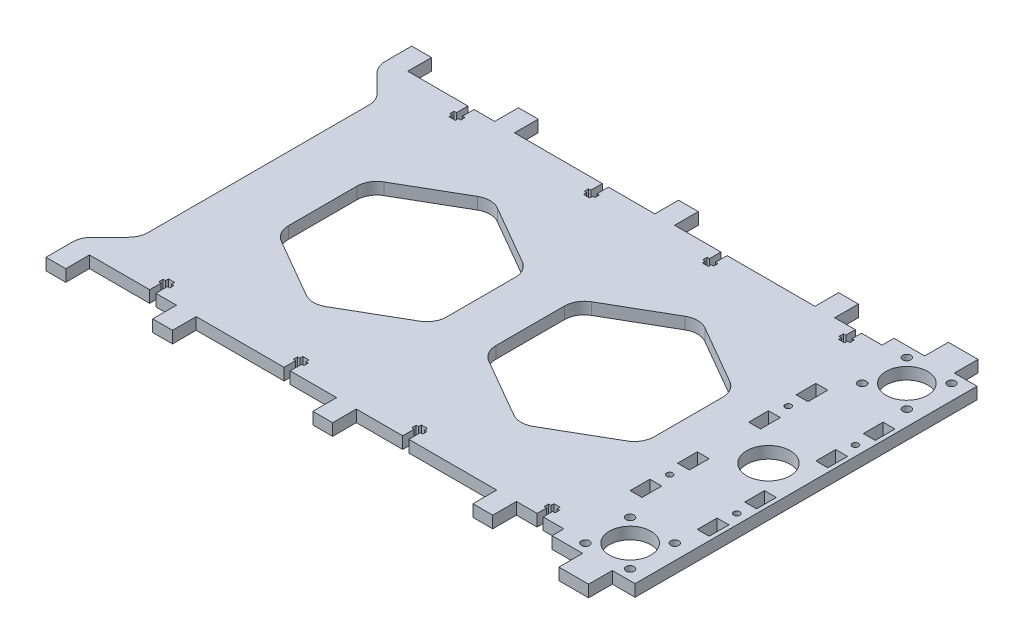
SolidWorks part; units mm, degrees
ref_plane "Спереди" through (0, 0, 0) normal (0, 0, 1) x (1, 0, 0)
ref_plane "Сверху" through (0, 0, 0) normal (0, 1, 0) x (1, 0, 0)
ref_plane "Справа" through (0, 0, 0) normal (1, 0, 0) x (0, 0, -1)
sketch "Эскиз1" plane through (0, 0, 0) normal (0, 1, 0) x (1, 0, 0)
  line L0 (138.7789, 22.6105) -> (144.7789, 22.6105)
  line L1 (138.7789, 12.6105) -> (138.7789, 22.6105)
  line L2 (144.7789, 12.6105) -> (138.7789, 12.6105)
  line L3 (144.7789, 22.6105) -> (144.7789, 12.6105)
  line L4 (138.7789, 36.6105) -> (138.7789, 46.6105)
  line L5 (144.7789, 36.6105) -> (138.7789, 36.6105)
  line L6 (144.7789, 46.6105) -> (144.7789, 36.6105)
  line L7 (138.7789, 46.6105) -> (144.7789, 46.6105)
  line L8 (104.7789, 46.6105) -> (110.7789, 46.6105)
  line L9 (104.7789, 36.6105) -> (104.7789, 46.6105)
  line L10 (110.7789, 36.6105) -> (104.7789, 36.6105)
  line L11 (110.7789, 46.6105) -> (110.7789, 36.6105)
  line L12 (110.7789, 12.6105) -> (104.7789, 12.6105)
  line L13 (110.7789, 22.6105) -> (110.7789, 12.6105)
  line L14 (104.7789, 22.6105) -> (110.7789, 22.6105)
  line L15 (104.7789, 12.6105) -> (104.7789, 22.6105)
  line L16 (144.7789, -13.3895) -> (138.7789, -13.3895)
  line L17 (138.7789, -13.3895) -> (138.7789, -23.3895)
  line L18 (138.7789, -23.3895) -> (144.7789, -23.3895)
  line L19 (144.7789, -23.3895) -> (144.7789, -13.3895)
  line L20 (144.7789, -47.3894) -> (144.7789, -37.3895)
  line L21 (144.7789, -37.3895) -> (138.7789, -37.3895)
  line L22 (138.7789, -37.3895) -> (138.7789, -47.3894)
  line L23 (138.7789, -47.3894) -> (144.7789, -47.3894)
  line L24 (110.7789, -37.3895) -> (104.7789, -37.3895)
  line L25 (104.7789, -37.3895) -> (104.7789, -47.3894)
  line L26 (104.7789, -47.3894) -> (110.7789, -47.3894)
  line L27 (110.7789, -47.3894) -> (110.7789, -37.3895)
  line L28 (104.7789, -23.3895) -> (110.7789, -23.3895)
  line L29 (110.7789, -23.3895) -> (110.7789, -13.3895)
  line L30 (110.7789, -13.3895) -> (104.7789, -13.3895)
  line L31 (104.7789, -13.3895) -> (104.7789, -23.3895)
  line L32 (-22.7211, 25.5913) -> (-52.7211, 42.9118)
  line L33 (-62.7211, 42.9118) -> (-92.7211, 25.5913)
  line L34 (-97.7211, 16.9311) -> (-97.7211, -17.71)
  line L35 (-92.7211, -26.3702) -> (-62.7211, -43.6907)
  line L36 (-52.7211, -43.6907) -> (-22.7211, -26.3702)
  line L37 (-17.7211, -17.71) -> (-17.7211, 16.9311)
  line L38 (12.2789, -26.3702) -> (42.2789, -43.6907)
  line L39 (52.2789, -43.6907) -> (82.2789, -26.3702)
  line L40 (87.2789, -17.71) -> (87.2789, 16.9311)
  line L41 (82.2789, 25.5913) -> (52.2789, 42.9118)
  line L42 (42.2789, 42.9118) -> (12.2789, 25.5913)
  line L43 (7.2789, 16.9311) -> (7.2789, -17.71)
  line L44 (-130.2211, -56.2473) -> (-130.2211, 55.4684)
  line L45 (-133.15, 62.5395) -> (-142.2922, 71.6816)
  line L46 (-145.2211, 92.1105) -> (-145.2211, 78.7527)
  line L47 (-145.2211, 92.1105) -> (-135.2211, 92.1105)
  line L48 (-135.2211, 92.1105) -> (-135.2211, 80.1105)
  line L49 (-135.2211, 80.1105) -> (-104.7711, 80.1105)
  line L50 (-104.7711, 80.1105) -> (-104.7711, 74.3105)
  line L51 (-104.7711, 74.3105) -> (-105.9711, 74.3105)
  line L52 (-105.9711, 74.3105) -> (-105.9711, 72.1105)
  line L53 (-105.9711, 72.1105) -> (-104.7711, 72.1105)
  line L54 (-104.7711, 72.1105) -> (-104.7711, 70.6105)
  line L55 (-104.7711, 70.6105) -> (-101.6711, 70.6105)
  line L56 (-101.6711, 70.6105) -> (-101.6711, 72.1105)
  line L57 (-101.6711, 72.1105) -> (-100.4711, 72.1105)
  line L58 (-100.4711, 72.1105) -> (-100.4711, 74.3105)
  line L59 (-100.4711, 74.3105) -> (-101.6711, 74.3105)
  line L60 (-101.6711, 74.3105) -> (-101.6711, 80.1105)
  line L61 (-101.6711, 80.1105) -> (-91.2211, 80.1105)
  line L62 (-91.2211, 80.1105) -> (-91.2211, 92.1105)
  line L63 (-91.2211, 92.1105) -> (-81.2211, 92.1105)
  line L64 (-81.2211, 92.1105) -> (-81.2211, 80.1105)
  line L65 (-81.2211, 80.1105) -> (-36.7711, 80.1105)
  line L66 (-36.7711, 80.1105) -> (-36.7711, 74.3105)
  line L67 (-36.7711, 74.3105) -> (-37.9711, 74.3105)
  line L68 (-37.9711, 74.3105) -> (-37.9711, 72.1105)
  line L69 (-37.9711, 72.1105) -> (-36.7711, 72.1105)
  line L70 (-36.7711, 72.1105) -> (-36.7711, 70.6105)
  line L71 (-36.7711, 70.6105) -> (-33.6711, 70.6105)
  line L72 (-33.6711, 70.6105) -> (-33.6711, 72.1105)
  line L73 (-33.6711, 72.1105) -> (-32.4711, 72.1105)
  line L74 (-32.4711, 72.1105) -> (-32.4711, 74.3105)
  line L75 (-32.4711, 74.3105) -> (-33.6711, 74.3105)
  line L76 (-33.6711, 74.3105) -> (-33.6711, 80.1105)
  line L77 (-33.6711, 80.1105) -> (-10.2211, 80.1105)
  line L78 (-10.2211, 80.1105) -> (-10.2211, 92.1105)
  line L79 (-10.2211, 92.1105) -> (-0.2211, 92.1105)
  line L80 (-0.2211, 92.1105) -> (-0.2211, 80.1105)
  line L81 (-0.2211, 80.1105) -> (23.2289, 80.1105)
  line L82 (23.2289, 80.1105) -> (23.2289, 74.3105)
  line L83 (23.2289, 74.3105) -> (22.0289, 74.3105)
  line L84 (22.0289, 74.3105) -> (22.0289, 72.1105)
  line L85 (22.0289, 72.1105) -> (23.2289, 72.1105)
  line L86 (23.2289, 72.1105) -> (23.2289, 70.6105)
  line L87 (23.2289, 70.6105) -> (26.3289, 70.6105)
  line L88 (26.3289, 70.6105) -> (26.3289, 72.1105)
  line L89 (26.3289, 72.1105) -> (27.5289, 72.1105)
  line L90 (27.5289, 72.1105) -> (27.5289, 74.3105)
  line L91 (27.5289, 74.3105) -> (26.3289, 74.3105)
  line L92 (26.3289, 74.3105) -> (26.3289, 80.1105)
  line L93 (26.3289, 80.1105) -> (70.7789, 80.1105)
  line L94 (70.7789, 80.1105) -> (70.7789, 92.1105)
  line L95 (70.7789, 92.1105) -> (80.7789, 92.1105)
  line L96 (80.7789, 92.1105) -> (80.7789, 80.1105)
  line L97 (80.7789, 80.1105) -> (91.2289, 80.1105)
  line L98 (91.2289, 80.1105) -> (91.2289, 75.3105)
  line L99 (91.2289, 75.3105) -> (90.0289, 75.3105)
  line L100 (90.0289, 75.3105) -> (90.0289, 73.1105)
  line L101 (90.0289, 73.1105) -> (91.2289, 73.1105)
  line L102 (91.2289, 73.1105) -> (91.2289, 71.6105)
  line L103 (91.2289, 71.6105) -> (94.3289, 71.6105)
  line L104 (94.3289, 71.6105) -> (94.3289, 73.1105)
  line L105 (94.3289, 73.1105) -> (95.5289, 73.1105)
  line L106 (95.5289, 73.1105) -> (95.5289, 75.3105)
  line L107 (95.5289, 75.3105) -> (94.3289, 75.3105)
  line L108 (94.3289, 75.3105) -> (94.3289, 80.1105)
  line L109 (94.3289, 80.1105) -> (104.7789, 80.1105)
  line L110 (104.7789, 80.1105) -> (104.7789, 86.1105)
  line L111 (104.7789, 86.1105) -> (120.2789, 86.1105)
  line L112 (120.2789, 86.1105) -> (120.2789, 98.1105)
  line L113 (120.2789, 98.1105) -> (135.2789, 98.1105)
  line L114 (135.2789, 98.1105) -> (135.2789, 86.1105)
  line L115 (135.2789, 86.1105) -> (146.7789, 86.1105)
  line L116 (146.7789, -86.8894) -> (146.7789, 86.1105)
  line L117 (135.2789, -86.8894) -> (146.7789, -86.8894)
  line L118 (135.2789, -98.8894) -> (135.2789, -86.8894)
  line L119 (120.2789, -98.8894) -> (135.2789, -98.8894)
  line L120 (120.2789, -86.8894) -> (120.2789, -98.8894)
  line L121 (104.7789, -86.8894) -> (120.2789, -86.8894)
  line L122 (104.7789, -80.8895) -> (104.7789, -86.8894)
  line L123 (94.3289, -80.8895) -> (104.7789, -80.8895)
  line L124 (94.3289, -76.0895) -> (94.3289, -80.8895)
  line L125 (95.5289, -76.0895) -> (94.3289, -76.0895)
  line L126 (95.5289, -73.8895) -> (95.5289, -76.0895)
  line L127 (94.3289, -73.8895) -> (95.5289, -73.8895)
  line L128 (94.3289, -72.3894) -> (94.3289, -73.8895)
  line L129 (91.2289, -72.3894) -> (94.3289, -72.3894)
  line L130 (91.2289, -73.8895) -> (91.2289, -72.3894)
  line L131 (90.0289, -73.8895) -> (91.2289, -73.8895)
  line L132 (90.0289, -76.0895) -> (90.0289, -73.8895)
  line L133 (91.2289, -76.0895) -> (90.0289, -76.0895)
  line L134 (91.2289, -80.8895) -> (91.2289, -76.0895)
  line L135 (80.7789, -80.8895) -> (91.2289, -80.8895)
  line L136 (80.7789, -92.8895) -> (80.7789, -80.8895)
  line L137 (70.7789, -92.8895) -> (80.7789, -92.8895)
  line L138 (70.7789, -80.8895) -> (70.7789, -92.8895)
  line L139 (26.3289, -80.8895) -> (70.7789, -80.8895)
  line L140 (26.3289, -75.0894) -> (26.3289, -80.8895)
  line L141 (27.5289, -75.0894) -> (26.3289, -75.0894)
  line L142 (27.5289, -72.8894) -> (27.5289, -75.0894)
  line L143 (26.3289, -72.8894) -> (27.5289, -72.8894)
  line L144 (26.3289, -71.3895) -> (26.3289, -72.8894)
  line L145 (23.2289, -71.3895) -> (26.3289, -71.3895)
  line L146 (23.2289, -72.8894) -> (23.2289, -71.3895)
  line L147 (22.0289, -72.8894) -> (23.2289, -72.8894)
  line L148 (22.0289, -75.0894) -> (22.0289, -72.8894)
  line L149 (23.2289, -75.0894) -> (22.0289, -75.0894)
  line L150 (23.2289, -80.8895) -> (23.2289, -75.0894)
  line L151 (-0.2211, -80.8895) -> (23.2289, -80.8895)
  line L152 (-0.2211, -92.8895) -> (-0.2211, -80.8895)
  line L153 (-10.2211, -92.8895) -> (-0.2211, -92.8895)
  line L154 (-10.2211, -80.8895) -> (-10.2211, -92.8895)
  line L155 (-33.6711, -80.8895) -> (-10.2211, -80.8895)
  line L156 (-33.6711, -75.0894) -> (-33.6711, -80.8895)
  line L157 (-32.4711, -75.0894) -> (-33.6711, -75.0894)
  line L158 (-32.4711, -72.8894) -> (-32.4711, -75.0894)
  line L159 (-33.6711, -72.8894) -> (-32.4711, -72.8894)
  line L160 (-33.6711, -71.3895) -> (-33.6711, -72.8894)
  line L161 (-36.7711, -71.3895) -> (-33.6711, -71.3895)
  line L162 (-36.7711, -72.8894) -> (-36.7711, -71.3895)
  line L163 (-37.9711, -72.8894) -> (-36.7711, -72.8894)
  line L164 (-37.9711, -75.0894) -> (-37.9711, -72.8894)
  line L165 (-36.7711, -75.0894) -> (-37.9711, -75.0894)
  line L166 (-36.7711, -80.8895) -> (-36.7711, -75.0894)
  line L167 (-81.2211, -80.8895) -> (-36.7711, -80.8895)
  line L168 (-81.2211, -92.8895) -> (-81.2211, -80.8895)
  line L169 (-91.2211, -92.8895) -> (-81.2211, -92.8895)
  line L170 (-91.2211, -80.8895) -> (-91.2211, -92.8895)
  line L171 (-101.6711, -80.8895) -> (-91.2211, -80.8895)
  line L172 (-101.6711, -75.0894) -> (-101.6711, -80.8895)
  line L173 (-100.4711, -75.0894) -> (-101.6711, -75.0894)
  line L174 (-100.4711, -72.8894) -> (-100.4711, -75.0894)
  line L175 (-101.6711, -72.8894) -> (-100.4711, -72.8894)
  line L176 (-101.6711, -71.3895) -> (-101.6711, -72.8894)
  line L177 (-104.7711, -71.3895) -> (-101.6711, -71.3895)
  line L178 (-104.7711, -72.8894) -> (-104.7711, -71.3895)
  line L179 (-105.9711, -72.8894) -> (-104.7711, -72.8894)
  line L180 (-105.9711, -75.0894) -> (-105.9711, -72.8894)
  line L181 (-104.7711, -75.0894) -> (-105.9711, -75.0894)
  line L182 (-104.7711, -80.8895) -> (-104.7711, -75.0894)
  line L183 (-135.2211, -80.8895) -> (-104.7711, -80.8895)
  line L184 (-135.2211, -92.8895) -> (-135.2211, -80.8895)
  line L185 (-145.2211, -92.8895) -> (-135.2211, -92.8895)
  line L186 (-142.2922, -72.4605) -> (-133.15, -63.3184)
  line L187 (-145.2211, -79.5316) -> (-145.2211, -92.8895)
  circle A0 centre (107.7789, 29.6105) radius 1.55
  circle A1 centre (116.4789, 58.3105) radius 2.05
  circle A2 centre (139.0789, 58.3105) radius 2.05
  circle A3 centre (127.7789, 69.6105) radius 10.5
  circle A4 centre (141.7789, 29.6105) radius 1.55
  circle A5 centre (139.0789, 80.9105) radius 2.05
  circle A6 centre (116.4789, 80.9105) radius 2.05
  circle A7 centre (107.7789, -30.3895) radius 1.55
  circle A8 centre (116.4789, -59.0895) radius 2.05
  circle A9 centre (139.0789, -59.0895) radius 2.05
  circle A10 centre (127.7789, -70.3895) radius 10.5
  circle A11 centre (141.7789, -30.3895) radius 1.55
  circle A12 centre (139.0789, -81.6895) radius 2.05
  circle A13 centre (116.4789, -81.6895) radius 2.05
  circle A14 centre (127.7789, -0.3895) radius 11
  arc A15 (-17.7211, 16.9311) -> (-22.7211, 25.5913) centre (-27.7211, 16.9311) ccw
  arc A16 (-52.7211, 42.9118) -> (-62.7211, 42.9118) centre (-57.7211, 34.2516) ccw
  arc A17 (-92.7211, 25.5913) -> (-97.7211, 16.9311) centre (-87.7211, 16.9311) ccw
  arc A18 (-97.7211, -17.71) -> (-92.7211, -26.3702) centre (-87.7211, -17.71) ccw
  arc A19 (-62.7211, -43.6907) -> (-52.7211, -43.6907) centre (-57.7211, -35.0305) ccw
  arc A20 (-22.7211, -26.3702) -> (-17.7211, -17.71) centre (-27.7211, -17.71) ccw
  arc A21 (7.2789, -17.71) -> (12.2789, -26.3702) centre (17.2789, -17.71) ccw
  arc A22 (42.2789, -43.6907) -> (52.2789, -43.6907) centre (47.2789, -35.0305) ccw
  arc A23 (82.2789, -26.3702) -> (87.2789, -17.71) centre (77.2789, -17.71) ccw
  arc A24 (87.2789, 16.9311) -> (82.2789, 25.5913) centre (77.2789, 16.9311) ccw
  arc A25 (52.2789, 42.9118) -> (42.2789, 42.9118) centre (47.2789, 34.2516) ccw
  arc A26 (12.2789, 25.5913) -> (7.2789, 16.9311) centre (17.2789, 16.9311) ccw
  arc A27 (-133.15, -63.3184) -> (-130.2211, -56.2473) centre (-140.2211, -56.2473) ccw
  arc A28 (-130.2211, 55.4684) -> (-133.15, 62.5395) centre (-140.2211, 55.4684) ccw
  arc A29 (-145.2211, 78.7527) -> (-142.2922, 71.6816) centre (-135.2211, 78.7527) ccw
  arc A30 (-142.2922, -72.4605) -> (-145.2211, -79.5316) centre (-135.2211, -79.5316) ccw
extrude "Бобышка-Вытянуть1" add sketch "Эскиз1" along normal blind 6
